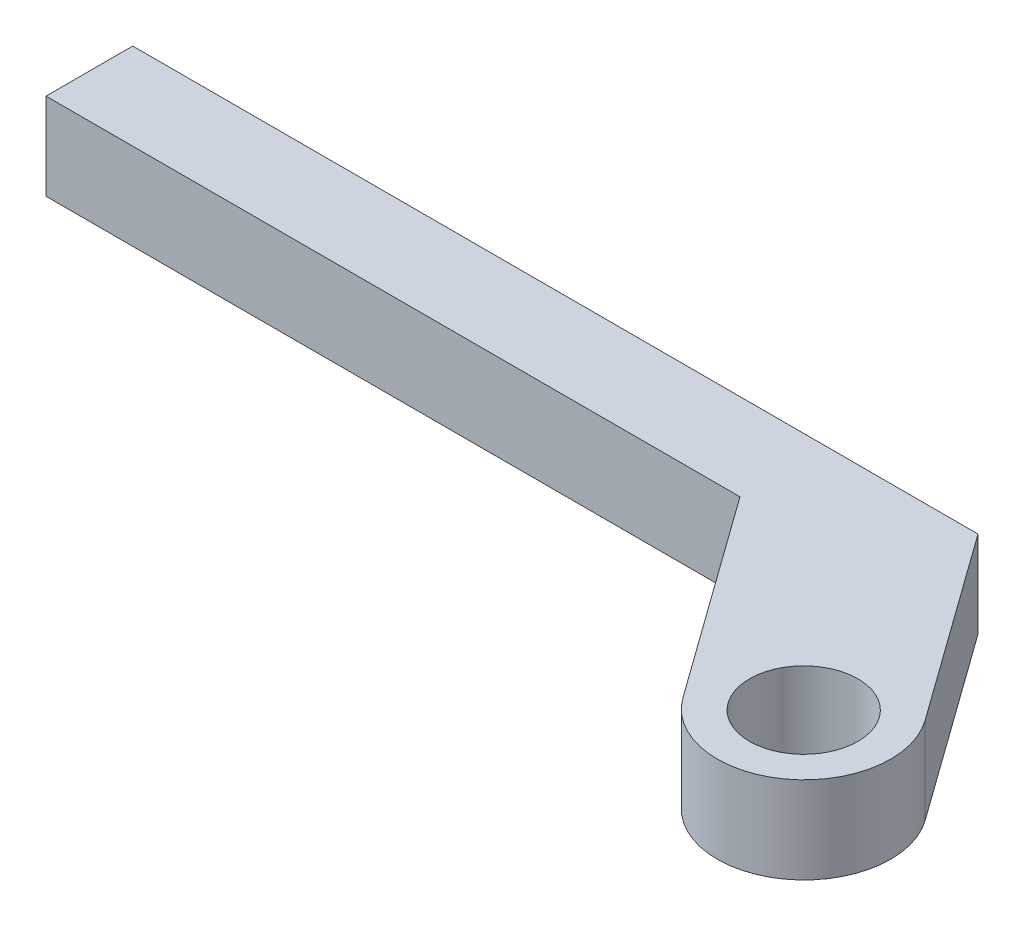
SolidWorks part; units mm, degrees
ref_plane "Front Plane" through (0, 0, 0) normal (0, 0, 1) x (1, 0, 0)
ref_plane "Top Plane" through (0, 0, 0) normal (0, 1, 0) x (1, 0, 0)
ref_plane "Right Plane" through (0, 0, 0) normal (1, 0, 0) x (0, 0, -1)
sketch "Sketch2" plane through (0, 0, 0) normal (0, 1, 0) x (1, 0, 0)
  line L20 (5.1633, -17.7805) -> (-45.4817, -17.7805) construction
  line L21 (-10.6389, -0.318) -> (0.0062, -15.1354)
  line L22 (-61.4389, -0.318) -> (-10.6389, -0.318)
  line L23 (-61.4389, 6.032) -> (-61.4389, -0.318)
  line L24 (-61.4389, 6.032) -> (-10.6389, 6.032)
  line L25 (-10.6389, 6.032) -> (0.4368, 6.032)
  line L26 (10.3205, -7.7255) -> (0.4368, 6.032)
  arc A3 (0.0062, -15.1354) -> (10.3205, -7.7255) centre (5.1633, -11.4305) ccw
extrude "Boss-Extrude1" add sketch "Sketch2" along normal blind 6.35
hole_wizard "3/8-16 Tapped Hole1" positions "Sketch3" profile "Sketch4" tap size "3/8-16" standard "ANSI Inch"
sketch "Sketch3" plane through (0, 6.35, 0) normal (0, 1, 0) x (1, 0, 0)
  line L1 (-10.6389, -0.318) -> (0.0062, -15.1354) construction
  line L2 (5.1633, -17.7805) -> (-27.2831, -17.7805) construction
  arc A1 (0.0062, -15.1354) -> (10.3205, -7.7255) centre (5.1633, -11.4305) ccw construction
  point P0 (5.2187, -11.5076)
  point P20 (8.8683, -16.5876)
  dimension "D1" = 6.35
  dimension "D2" = 5.08
sketch "Sketch4" plane through (5.2187, 6.35, 11.5076) normal (1, 0, 0) x (0, 0, 1)
  line L0 (0, 0) -> (0, 8.7347)
  line L1 (0, 8.7347) -> (3.9687, 6.35)
  line L2 (3.9687, 6.35) -> (3.9688, 0)
  line L5 (3.9688, 0) -> (0, 0)
  line L10 (0, 8.7347) -> (-3.9688, 6.35) construction
  line L11 (0, -6.35) -> (0, 107.95) construction
  dimension "Tap Drill Dia." = 7.9375
  dimension "Tap Drill Depth" = 6.35
  dimension "Drill Angle" = 118
cosmetic thread "Hole Thread1" parameters "D1"=19.05, "D2"=9.525
